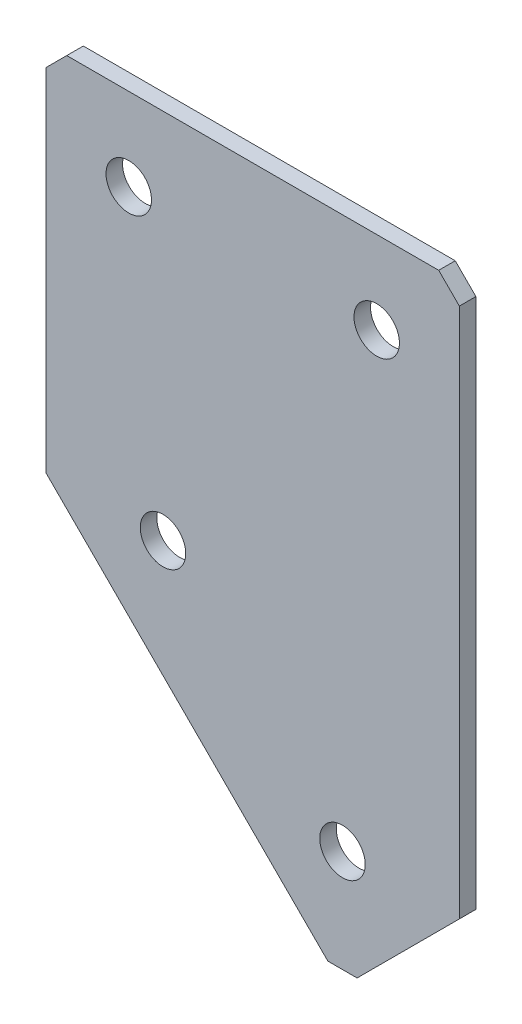
SolidWorks part; units mm, degrees
material "Простая углеродистая сталь"
ref_plane "Спереди" through (0, 0, 0) normal (0, 0, 1) x (1, 0, 0)
ref_plane "Сверху" through (0, 0, 0) normal (0, 1, 0) x (1, 0, 0)
ref_plane "Справа" through (0, 0, 0) normal (1, 0, 0) x (0, 0, -1)
sketch "Эскиз3" plane through (0, 0, 0) normal (0, 0, -1) x (1, 0, 0)
  line L0 (0, 0) -> (50, 0)
  line L1 (50, 0) -> (50, 66.7157)
  line L2 (0, 0) -> (0, 45)
  line L3 (0, 45) -> (35.8579, 80.8579)
  line L4 (35.8579, 80.8579) -> (50, 66.7157)
  dimension "D1" = 50
  dimension "D2" = 45
  dimension "D3" = 20
  dimension "D4" = 45
  dimension "D5" = 66.7157
extrude "Бобышка-Вытянуть1" add sketch "Эскиз3" along normal blind 2
hole_wizard "Отверстие с зазором M51" positions "Эскиз4" profile "Эскиз5" hole size "M5" standard "DIN" end condition through all
sketch "Эскиз4" plane through (0, 0, -2) normal (0, 0, -1) x (1, 0, 0)
  line L0 (14.1421, 45) -> (35.8579, 66.7157) construction
  line L2 (35.8579, 80.8579) -> (0, 45) construction
  line L3 (10, 10) -> (40, 10) construction
  line L5 (0, 0) -> (50, 0) construction
  line L6 (0, 45) -> (0, 0) construction
  line L7 (50, 0) -> (50, 66.7157) construction
  line L8 (50, 66.7157) -> (35.8579, 80.8579) construction
  line L9 (14.1421, 45) -> (0, 30.8579) construction
  point P0 (10, 10)
  point P2 (40, 10)
  point P4 (14.1421, 45)
  point P6 (35.8579, 66.7157)
  dimension "D1" = 10
  dimension "D2" = 10
  dimension "D3" = 10
  dimension "D4" = 10
  dimension "D5" = 10
  dimension "D6" = 20
  dimension "D7" = 30.7107
  dimension "D8" = 30
sketch "Эскиз5" plane through (10, -10, -2) normal (1, 0, 0) x (0, 1, 0)
  line L0 (0, 0) -> (0, 2)
  line L1 (0, 2) -> (2.75, 2)
  line L2 (2.75, 2) -> (2.75, 0)
  line L5 (2.75, 0) -> (0, 0)
  line L11 (0, -6.35) -> (0, 107.95) construction
  dimension "Диаметр сквозного отверстия" = 5.5
  dimension "Глубина сквозного отверстия" = 2
chamfer "Фаска1" distance 2.5 distance2 2.5 3 edges at (35.8579, -80.8579, -1) (50, 0, -1) (0, 0, -1)
